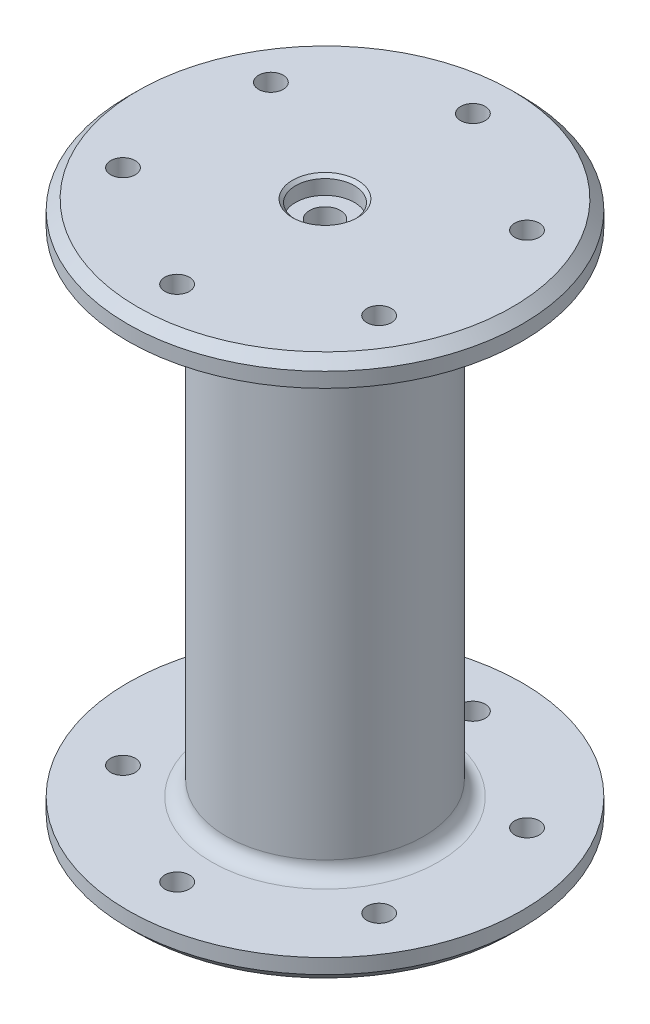
SolidWorks part; units mm, degrees
ref_plane "Front Plane" through (0, 0, 0) normal (0, 0, 1) x (1, 0, 0)
ref_plane "Top Plane" through (0, 0, 0) normal (0, 1, 0) x (1, 0, 0)
ref_plane "Right Plane" through (0, 0, 0) normal (1, 0, 0) x (0, 0, -1)
sketch "Sketch1" plane through (0, 0, 0) normal (0, 1, 0) x (1, 0, 0)
  circle A0 centre (0, 0) radius 20
  dimension "ShaftDiameter" = 40
extrude "Boss-Extrude1" add sketch "Sketch1" along normal mid plane 100
sketch "Sketch2" plane through (0, 50, 0) normal (0, 1, 0) x (1, 0, 0)
  circle A0 centre (0, 0) radius 40
  dimension "CapDiameter" = 80
extrude "Boss-Extrude2" add sketch "Sketch2" along normal blind 5
chamfer "Chamfer1" distance 2 angle 45 1 edges at (0, 55, 40)
sketch "Sketch3" plane through (0, 55, 0) normal (0, 1, 0) x (1, 0, 0)
  line L0 (0, 20) -> (0, 40) construction
  circle A0 centre (0, 0) radius 20 construction
  circle A2 centre (0, 0) radius 40 construction
  circle A3 centre (0, 30) radius 2.5
  dimension "D1" = 5
extrude "Cut-Extrude1" cut sketch "Sketch3" against normal blind 295 and the other way blind 395
pattern_circular "CirPattern1" count 6 every 60 about axis through (0, 0, 0) along (0, 1, 0) of "Cut-Extrude1"
fillet "Fillet1" radius 3 1 edges at (0, 50, 20)
hole_wizard "CBORE for #12 Binding Head Machine Screw1" positions "Sketch4" profile "Sketch5" counterbore size "#12" standard "ANSI Inch"
sketch "Sketch4" plane through (0, 55, 0) normal (0, 1, 0) x (1, 0, 0)
  point P0 (0, 0)
sketch "Sketch5" plane through (0, 55, 0) normal (1, 0, 0) x (0, 0, 1)
  line L0 (0, 0) -> (0, 1.9272)
  line L1 (0, 1.9272) -> (3.1242, 0.05)
  line L2 (3.1242, 0.05) -> (3.1242, 3.5814)
  line L3 (3.1242, 3.5814) -> (5.9538, 3.5814)
  line L5 (5.9538, 3.5814) -> (5.9538, 0.635)
  line L6 (5.9538, 0.635) -> (6.5888, 0)
  line L7 (6.5888, 0) -> (0, 0)
  line L8 (-5.9538, 0.635) -> (-6.5888, 0) construction
  line L10 (0, 1.9272) -> (-3.1242, 0.05) construction
  line L11 (0, -6.35) -> (0, 107.95) construction
  dimension "Hole Dia." = 6.2484
  dimension "Hole Depth" = 0.05
  dimension "C'Bore Dia." = 11.9075
  dimension "C'Bore Depth" = 3.5814
  dimension "Near C'Sink Dia." = 13.1775
  dimension "Near C'Sink Angle" = 90
  dimension "Drill Angle" = 118
sketch "Sketch6" plane through (0, 51.4186, 0) normal (0, 1, 0) x (1, 0, 0)
  circle A0 centre (0, 0) radius 3.125
  circle A1 centre (0, 0) radius 38 construction
  dimension "D1" = 6.25
extrude "Cut-Extrude2" cut sketch "Sketch6" against normal through all both and the other way through all
mirror "Mirror3" about plane through (0, 0, 0) normal (0, 1, 0) of "Cut-Extrude2", "Boss-Extrude2", "Fillet1", "Chamfer1", "CBORE for #12 Binding Head Machine Screw1"
mirror "Mirror4" about plane through (0, 0, 0) normal (0, 1, 0) of "CirPattern1", "Cut-Extrude1"
